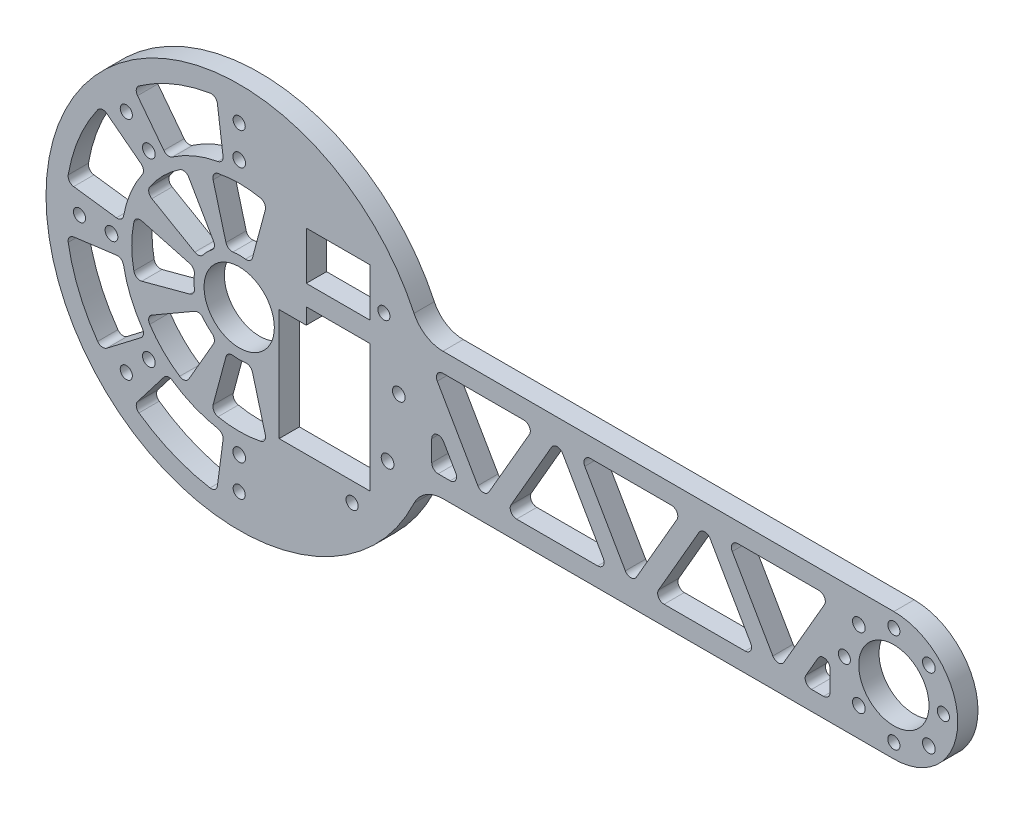
SolidWorks part; units mm, degrees
material "Balsa"
ref_plane "Front Plane" through (0, 0, 0) normal (0, 0, 1) x (1, 0, 0)
ref_plane "Top Plane" through (0, 0, 0) normal (0, 1, 0) x (1, 0, 0)
ref_plane "Right Plane" through (0, 0, 0) normal (1, 0, 0) x (0, 0, -1)
sketch "Sketch1" plane through (0, 0, 0) normal (0, 0, 1) x (1, 0, 0)
  line L0 (57.0986, -20) -> (205, -20)
  line L1 (57.0986, 20) -> (205, 20)
  line L2 (45.3154, 21.1309) -> (0, 0) construction
  line L3 (0, 0) -> (35.3553, -35.3553) construction
  line L4 (49.9788, 1.4542) -> (0, 0) construction
  line L5 (0, 0) -> (46.4674, -18.4603) construction
  arc A0 (57.0986, -20) -> (57.0986, 20) centre (0, 0) cw
  arc A1 (205, 20) -> (205, -20) centre (205, 0) cw
  circle A2 centre (0, 0) radius 60.5 construction
  circle A3 centre (0, 0) radius 11
  circle A4 centre (45.3154, 21.1309) radius 1.8986
  circle A5 centre (0, 0) radius 40 construction
  circle A6 centre (0, 0) radius 50 construction
  circle A7 centre (46.4674, -18.4603) radius 1.9939
  circle A8 centre (205, 0) radius 11
  circle A9 centre (49.9788, 1.4542) radius 1.9939
  circle A10 centre (205, 0) radius 15.5 construction
  circle A11 centre (205, -15.5) radius 1.8987
  circle A12 centre (215.9602, -10.9602) radius 1.9939
  circle A13 centre (189.5, 0) radius 1.8987
  circle A14 centre (194.0398, -10.9602) radius 1.9939
  circle A15 centre (205, 15.5) radius 1.8987
  circle A16 centre (194.0398, 10.9602) radius 1.9939
  circle A17 centre (220.5, 0) radius 1.8987
  circle A18 centre (215.9602, 10.9602) radius 1.9939
  circle A29 centre (0, -40) radius 1.9939
  circle A30 centre (0, -50) radius 1.8986
  circle A37 centre (-28.2843, -28.2843) radius 1.9939
  circle A38 centre (-35.3553, -35.3553) radius 1.8986
  circle A39 centre (-40, 0) radius 1.9939
  circle A40 centre (-50, 0) radius 1.8986
  circle A41 centre (-28.2843, 28.2843) radius 1.9939
  circle A42 centre (-35.3553, 35.3553) radius 1.8986
  circle A43 centre (0, 40) radius 1.9939
  circle A44 centre (0, 50) radius 1.8986
  circle A45 centre (28.2843, 28.2843) radius 1.9939 construction
  circle A46 centre (35.3553, 35.3553) radius 1.8986 construction
  circle A47 centre (40, 0) radius 1.9939 construction
  circle A48 centre (50, 0) radius 1.8986 construction
  circle A49 centre (28.2843, -28.2843) radius 1.9939 construction
  circle A50 centre (35.3553, -35.3553) radius 1.8986
  dimension "D1" = 121
  dimension "D4" = 22
  dimension "D6" = 100
  dimension "D7" = 80
  dimension "D8" = 70
  dimension "D9" = 3.7973
  dimension "D10" = 3.9878
  dimension "D15" = 3.7973
  dimension "D16" = 3.9878
  dimension "D17" = 3.7973
  dimension "D18" = 3.9878
  dimension "D5" = 31
  dimension "D19" = 3.9878
  dimension "D2" = 40
  dimension "D3" = 205
  dimension "D11" = 45
  dimension "D13" = 23.333
  dimension "D14" = 23.333
  dimension "D12" = 4
  dimension "D21" = 8
extrude "Boss-Extrude1" add sketch "Sketch1" along normal blind 6.35
fillet "Fillet1" radius 10 2 edges at (57.0986, -20, 3.175) (57.0986, 20, 3.175)
sketch "Sketch2" plane through (0, 0, 6.35) normal (0, 0, 1) x (1, 0, 0)
  line L0 (60.2923, 14) -> (92.624, 14)
  line L1 (92.624, 14) -> (76.4581, -14)
  line L2 (76.4581, -14) -> (60.2923, 14)
  line L3 (83.3864, -14) -> (99.5522, 14)
  line L4 (99.5522, 14) -> (115.718, -14)
  line L5 (115.718, -14) -> (83.3864, -14)
  line L6 (106.4804, 14) -> (122.6462, -14)
  line L7 (122.6462, -14) -> (138.812, 14)
  line L8 (138.812, 14) -> (106.4804, 14)
  line L9 (129.5744, -14) -> (145.7402, 14)
  line L10 (145.7402, 14) -> (161.906, -14)
  line L11 (161.906, -14) -> (129.5744, -14)
  line L12 (152.6684, 14) -> (168.8342, -14)
  line L13 (168.8342, -14) -> (185, 14)
  line L14 (185, 14) -> (152.6684, 14)
  line L15 (60.2923, 2) -> (60.2923, -14)
  line L16 (60.2923, -14) -> (69.5299, -14)
  line L17 (69.5299, -14) -> (60.2923, 2)
  line L18 (185, 2) -> (185, -14)
  line L19 (185, -14) -> (175.7624, -14)
  line L20 (175.7624, -14) -> (185, 2)
  line L21 (205, 20) -> (63.7985, 20) construction
  line L22 (63.7985, -20) -> (205, -20) construction
  arc A0 (205, -20) -> (205, 20) centre (205, 0) ccw construction
  point P25 (225, 0)
  dimension "D1" = 60
  dimension "D2" = 60
  dimension "D3" = 6
  dimension "D4" = 6
  dimension "D5" = 6
  dimension "D6" = 6
  dimension "D7" = 6
  dimension "D8" = 6
  dimension "D9" = 6
  dimension "D10" = 6
  dimension "D11" = 40
extrude "Cut-Extrude1" cut sketch "Sketch2" against normal through all
fillet "Fillet2" radius 2 21 edges at (175.7624, -14, 3.175) (69.5299, -14, 3.175) (129.5744, -14, 3.175) (83.3864, -14, 3.175) (122.6462, -14, 3.175) (76.4581, -14, 3.175) (60.2923, -14, 3.175) (60.2923, 2, 3.175) (99.5522, 14, 3.175) (145.7402, 14, 3.175) (185, 2, 3.175) (115.718, -14, 3.175) (161.906, -14, 3.175) (185, -14, 3.175) (168.8342, -14, 3.175) (185, 14, 3.175) (138.812, 14, 3.175) (92.624, 14, 3.175) (152.6684, 14, 3.175) (106.4804, 14, 3.175) (60.2923, 14, 3.175)
other "Move Face1" [suppressed] parameters "D1"=0.08
sketch "Sketch3" plane through (0, 0, 0) normal (0, 0, 1) x (1, 0, 0)
  line L0 (12.5, -29.35) -> (41, -29.35)
  line L1 (41, -29.35) -> (41, 10.65)
  line L5 (41, 17) -> (41, 32)
  line L6 (41, 32) -> (21, 32)
  line L7 (21, 32) -> (21, 17)
  line L8 (21, 17) -> (41, 17)
  line L10 (41, 10.65) -> (21, 10.65)
  line L11 (21, 10.65) -> (21, 5.65)
  line L12 (21, 5.65) -> (12.5, 5.65)
  line L13 (12.5, 5.65) -> (12.5, -29.35)
  point P5 (31, 32)
  dimension "D2" = 20
  dimension "D3" = 6.35
  dimension "D4" = 15
  dimension "D5" = 40
  dimension "D6" = 21
  dimension "D8" = 5
  dimension "D10" = 8.5
  dimension "D11" = 32
extrude "Cut-Extrude2" cut sketch "Sketch3" along normal through all
sketch "Sketch4" plane through (0, 0, 6.35) normal (0, 0, 1) x (1, 0, 0)
  line L0 (-13.692, 3.6688) -> (-32.5034, 8.7093)
  line L1 (-32.5034, -8.7093) -> (-13.692, -3.6688)
  line L2 (0, 0) -> (-72.0801, 0) construction
  arc A0 (-13.692, -3.6688) -> (-13.692, 3.6688) centre (0, 0) cw
  arc A1 (-32.5034, -8.7093) -> (-32.5034, 8.7093) centre (0, 0) cw
  circle A2 centre (0, 0) radius 11 construction
  circle A3 centre (-40, 0) radius 1.9939 construction
  point P6 (-14.175, 0)
  point P10 (-33.65, 0)
  dimension "D2" = 3.175
  dimension "D3" = 6.35
  dimension "D1" = 30
extrude "Cut-Extrude3" cut sketch "Sketch4" against normal through all
fillet "Fillet4" radius 2 4 edges at (-32.5034, -8.7093, 3.175) (-13.692, -3.6688, 3.175) (-13.692, 3.6688, 3.175) (-32.5034, 8.7093, 3.175)
pattern_circular "CirPattern2" count 8 over 360 about axis through (0, 0, 0) along (0, 0, 1) skipping 3, 4, 5 of "Cut-Extrude3", "Fillet4"
sketch "Sketch5" plane through (0, 0, 6.35) normal (0, 0, 1) x (1, 0, 0)
  line L0 (0, 0) -> (-60.6345, 25.1156) construction
  line L1 (0, 0) -> (-72.6736, 0) construction
  line L2 (-43.0989, 33.071) -> (-29.2152, 22.4176)
  line L3 (-53.8602, 7.0908) -> (-36.51, 4.8066)
  arc A0 (-36.51, 4.8066) -> (-29.2152, 22.4176) centre (0, 0) cw
  arc A1 (-53.8602, 7.0908) -> (-43.0989, 33.071) centre (0, 0) cw
  circle A2 centre (-35.3553, 35.3553) radius 1.8987 construction
  circle A3 centre (-28.2843, 28.2843) radius 1.9939 construction
  circle A4 centre (-35.3553, 35.3553) radius 1.8986 construction
  circle A5 centre (-28.2843, 28.2843) radius 1.9939 construction
  arc A6 (-32.9888, 6.6379) -> (-32.9888, -6.6379) centre (0, 0) ccw construction
  arc A7 (54.7491, 25.7447) -> (54.7491, -25.7447) centre (0, 0) ccw construction
  point P14 (-50.1898, 20.7893)
  dimension "D3" = 3.175
  dimension "D4" = 6.175
  dimension "D1" = 22.5
  dimension "D2" = 30
extrude "Cut-Extrude4" cut sketch "Sketch5" against normal through all
fillet "Fillet5" radius 2 4 edges at (-53.8602, 7.0908, 3.175) (-36.51, 4.8066, 3.175) (-29.2152, 22.4176, 3.175) (-43.0989, 33.071, 3.175)
pattern_circular "CirPattern3" count 8 over 360 about axis through (0, 0, 0) along (0, 0, 1) skipping 2, 3, 4, 5 of "Cut-Extrude4", "Fillet5"
chamfer "Chamfer3" distance 2.301 angle 41 7 edges at (47.214, 21.1309, 0) (37.254, -35.3553, 0) (1.8986, -50, 0) (-33.4567, -35.3553, 0) (-48.1014, 0, 0) (-33.4567, 35.3553, 0) (1.8986, 50, 0)
